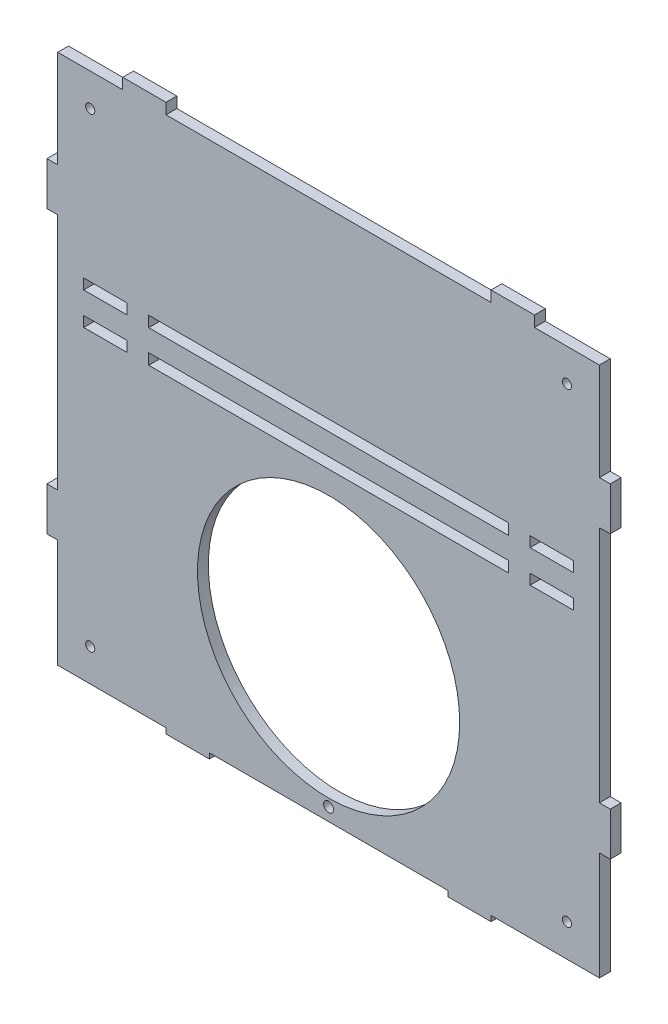
SolidWorks part; units mm, degrees
ref_plane "Front Plane" through (0, 0, 0) normal (0, 0, 1) x (1, 0, 0)
ref_plane "Top Plane" through (0, 0, 0) normal (0, 1, 0) x (1, 0, 0)
ref_plane "Right Plane" through (0, 0, 0) normal (1, 0, 0) x (0, 0, -1)
sketch "Sketch1" plane through (0, 0, 0) normal (0, 0, 1) x (1, 0, 0)
  line L0 (-130, -19.9) -> (-125, -19.9) construction
  line L1 (125, -69.9) -> (75, -69.9)
  line L2 (125, -69.9) -> (125, -19.9)
  line L3 (125, 180.1) -> (-125, 180.1)
  line L4 (-125, -69.9) -> (-125, -19.9)
  line L5 (-130, 0.1) -> (-130, -19.9) construction
  line L6 (-125, 0.1) -> (-130, 0.1) construction
  line L7 (-130, 110.1) -> (-125, 110.1) construction
  line L8 (-130, 130.1) -> (-130, 110.1) construction
  line L9 (-125, 130.1) -> (-130, 130.1) construction
  line L10 (125, 130.1) -> (130, 130.1) construction
  line L11 (130, 130.1) -> (130, 110.1) construction
  line L12 (130, 110.1) -> (125, 110.1) construction
  line L13 (130, -19.9) -> (125, -19.9) construction
  line L14 (130, 0.1) -> (130, -19.9) construction
  line L15 (125, 0.1) -> (130, 0.1) construction
  line L16 (-130, -19.9) -> (-125, -19.9)
  line L17 (-130, 0.1) -> (-130, -19.9)
  line L18 (-125, 0.1) -> (-130, 0.1)
  line L19 (-130, 110.1) -> (-125, 110.1)
  line L20 (-130, 130.1) -> (-130, 110.1)
  line L21 (-125, 130.1) -> (-130, 130.1)
  line L22 (125, 130.1) -> (130, 130.1)
  line L23 (130, 130.1) -> (130, 110.1)
  line L24 (130, 110.1) -> (125, 110.1)
  line L25 (130, -19.9) -> (125, -19.9)
  line L26 (130, 0.1) -> (130, -19.9)
  line L27 (125, 0.1) -> (130, 0.1)
  line L28 (55, -74.9) -> (55, -69.9) construction
  line L30 (75, -74.9) -> (75, -69.9) construction
  line L31 (-55, -74.9) -> (-55, -69.9) construction
  line L33 (-75, -74.9) -> (-75, -69.9) construction
  line L34 (55, -72.4) -> (55, -69.9)
  line L35 (-55, -72.4) -> (-75, -72.4)
  line L36 (75, -72.4) -> (75, -69.9)
  line L37 (-55, -72.4) -> (-55, -69.9)
  line L38 (75, -72.4) -> (55, -72.4)
  line L39 (-75, -72.4) -> (-75, -69.9)
  line L40 (-125, 180.1) -> (125, 180.1) construction
  line L41 (-125, 130.1) -> (-125, 180.1)
  line L42 (125, 130.1) -> (125, 180.1)
  line L43 (125, 0.1) -> (125, 110.1)
  line L44 (55, -69.9) -> (-55, -69.9)
  line L45 (-75, -69.9) -> (-125, -69.9)
  line L46 (-125, 0.1) -> (-125, 110.1)
  circle A0 centre (0, 0) radius 57.5 construction
  circle A1 centre (0, 0) radius 57.5 construction
  circle A2 centre (0, 0) radius 60.5
  circle A3 centre (0, -64) radius 2.3 construction
  circle A4 centre (0, -64) radius 2.3
  dimension "D3" = 2.5
  dimension "D1" = 0
  dimension "D2" = 3
  dimension "D4" = 2.5
extrude "Boss-Extrude1" add sketch "Sketch1" along normal blind 5
sketch "Sketch3" plane through (0, 0, 5) normal (0, 0, 1) x (1, 0, 0)
  line L0 (-113, 91.0052) -> (-113, 86.0052) construction
  line L1 (-113, 90.9052) -> (-93, 90.9052)
  line L2 (-113, 90.9052) -> (-113, 86.1052)
  line L3 (-113, 86.1052) -> (-93, 86.1052)
  line L4 (-93, 90.9052) -> (-93, 86.1052)
  line L5 (-93, 91.0052) -> (-93, 86.0052) construction
  line L6 (-113, 86.0052) -> (-93, 86.0052) construction
  line L7 (-113, 76.0052) -> (-113, 71.0052) construction
  line L8 (-113, 75.9052) -> (-93, 75.9052)
  line L9 (-113, 75.9052) -> (-113, 71.1052)
  line L10 (-113, 71.1052) -> (-93, 71.1052)
  line L11 (-93, 75.9052) -> (-93, 71.1052)
  line L12 (-93, 76.0052) -> (-93, 71.0052) construction
  line L13 (-113, 71.0052) -> (-93, 71.0052) construction
  dimension "D1" = 4.8
  dimension "D2" = 0.1
  dimension "D3" = 0.1
  dimension "D4" = 4.8
extrude "Cut-Extrude1" cut sketch "Sketch3" against normal blind 5
mirror "Mirror1" about plane through (0, 0, 0) normal (1, 0, 0) of "Cut-Extrude1"
sketch "Sketch4" plane through (0, 0, 5) normal (0, 0, 1) x (1, 0, 0)
  line L0 (60.3848, 86.0052) -> (80.6469, 86.0052) construction
  line L1 (-83, 91.0052) -> (83, 91.0052)
  line L2 (-83, 91.0052) -> (-83, 86.0052)
  line L3 (-83, 86.0052) -> (83, 86.0052)
  line L4 (83, 91.0052) -> (83, 86.0052)
  line L5 (93, 91.0052) -> (93, 86.0052) construction
  line L6 (-93, 91.0052) -> (-93, 86.0052) construction
  line L7 (-93, 76.0052) -> (-80.6469, 76.0052) construction
  line L8 (-83, 76.0052) -> (83, 76.0052)
  line L9 (-83, 76.0052) -> (-83, 71.0052)
  line L10 (-83, 71.0052) -> (83, 71.0052)
  line L11 (83, 76.0052) -> (83, 71.0052)
  line L12 (80.6469, 71.0052) -> (93, 71.0052) construction
  dimension "D1" = 5
  dimension "D2" = 10
  dimension "D3" = 10
  dimension "D4" = 5
extrude "Cut-Extrude2" cut sketch "Sketch4" against normal blind 5
sketch "Sketch5" plane through (0, 0, 5) normal (0, 0, 1) x (1, 0, 0)
  line L0 (-125, -69.9) -> (-75, -69.9) construction
  line L1 (-125, -19.9) -> (-125, -69.9) construction
  line L2 (75, -69.9) -> (125, -69.9) construction
  line L3 (125, -69.9) -> (125, -19.9) construction
  circle A0 centre (-110, -54.9) radius 2.1
  circle A1 centre (110, -54.9) radius 2.1
  dimension "D1" = 4.2
  dimension "D2" = 15
  dimension "D3" = 15
  dimension "D4" = 4.2
  dimension "D5" = 15
  dimension "D6" = 15
extrude "Cut-Extrude3" cut sketch "Sketch5" against normal blind 5
sketch "Sketch6" plane through (0, 0, 5) normal (0, 0, 1) x (1, 0, 0)
  line L0 (-125, 175.1) -> (-95, 175.1)
  line L1 (-125, -79.9) -> (-125, 180.1) construction
  line L2 (-95, 175.1) -> (-95, 180.1)
  line L3 (125, 180.1) -> (-125, 180.1) construction
  line L4 (-75, 180.1) -> (-75, 175.1)
  line L5 (-75, 175.1) -> (75, 175.1)
  line L6 (75, 175.1) -> (75, 180.1)
  line L7 (95, 180.1) -> (95, 175.1)
  line L8 (95, 175.1) -> (125, 175.1)
  line L9 (125, -79.9) -> (125, 180.1) construction
  line L10 (125, 175.1) -> (125, 180.1)
  line L11 (125, 180.1) -> (95, 180.1)
  line L12 (-125, 180.1) -> (-125, 130.1) construction
  line L13 (-125, 175.1) -> (-125, 180.1)
  line L14 (-125, 180.1) -> (-95, 180.1)
  line L15 (-75, 180.1) -> (75, 180.1)
  dimension "D1" = 20
  dimension "D2" = 5
  dimension "D3" = 20
  dimension "D4" = 30
  dimension "D5" = 30
extrude "Cut-Extrude4" cut sketch "Sketch6" against normal blind 5
sketch "Sketch7" plane through (0, 0, 5) normal (0, 0, 1) x (1, 0, 0)
  line L0 (-125, 175.1) -> (-125, 130.1) construction
  line L1 (-125, 175.1) -> (-95, 175.1) construction
  line L2 (125, 130.1) -> (125, 175.1) construction
  line L3 (95, 175.1) -> (125, 175.1) construction
  circle A0 centre (-110, 160.1) radius 2.1
  circle A1 centre (110, 160.1) radius 2.1
  dimension "D1" = 4.2
  dimension "D2" = 4.2
  dimension "D3" = 15
  dimension "D5" = 15
  dimension "D6" = 15
  dimension "D4" = 15
extrude "Cut-Extrude5" cut sketch "Sketch7" against normal blind 5
